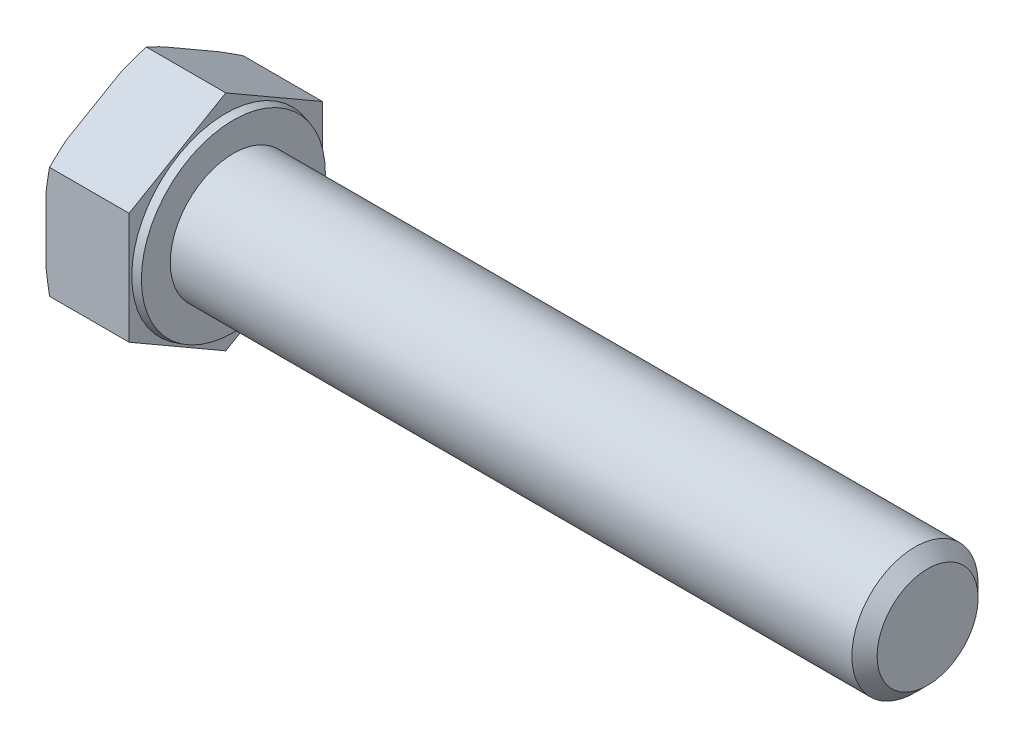
SolidWorks part; units mm, degrees
material "AISI 1020"
ref_plane "Спереди" through (0, 0, 0) normal (0, 0, 1) x (1, 0, 0)
ref_plane "Сверху" through (0, 0, 0) normal (0, 1, 0) x (1, 0, 0)
ref_plane "Справа" through (0, 0, 0) normal (1, 0, 0) x (0, 0, -1)
sketch "Эскиз1" plane through (0, 0, 0) normal (0, 0, 1) x (1, 0, 0)
  line L0 (-1000, 0) -> (49000, 0) construction
  line L1 (-6.58, 0) -> (-6.58, 8.85)
  line L2 (-6.58, 8.85) -> (0, 8.85)
  line L3 (0, 8.85) -> (0, 7.449)
  line L4 (0.6, 5) -> (55.6, 5)
  line L5 (55.6, 5) -> (55.6, 0)
  line L6 (-6.58, 0) -> (55.6, 0)
  line L7 (0, 7.449) -> (0.6, 7.2882)
  line L8 (0.6, 7.2882) -> (0.6, 5)
  line L9 (0.5, 0) -> (0.5, 7.315) construction
  dimension "_d" = 10
  dimension "D1" = 55
  dimension "D5" = 17.7
  dimension "D2" = 0.6
  dimension "D3" = 6.58
  dimension "D4" = 0.1
  dimension "D6" = 14.63
  dimension "D7" = 75
revolve "Повернуть1" add sketch "Эскиз1" angle 360 about L0
sketch "Эскиз2" plane through (-6.58, 0, 0) normal (-1, 0, 0) x (0, 0, 1)
  line L1 (0, -8.85) -> (7.6643, -4.425)
  line L2 (7.6643, -4.425) -> (7.6643, 4.425)
  line L3 (7.6643, 4.425) -> (0, 8.85)
  line L4 (0, 8.85) -> (-7.6643, 4.425)
  line L5 (-7.6643, 4.425) -> (-7.6643, -4.425)
  line L6 (-7.6643, -4.425) -> (0, -8.85)
  circle A0 centre (0, 0) radius 7.6643 construction
  circle A1 centre (0, 0) radius 8.85 construction
extrude "Вырез-Вытянуть1" cut sketch "Эскиз2" against normal through all flip side to cut
sketch "Эскиз4" plane through (0, 0, 0) normal (0, 0, 1) x (1, 0, 0)
  line L0 (-1000, 0) -> (49000, 0) construction
  line L1 (-6.58, 8.075) -> (-6.2979, 8.85)
  line L2 (-6.2979, 8.85) -> (-6.58, 8.85)
  line L3 (-6.58, 8.85) -> (-6.58, 8.075)
  line L4 (-6.58, 4.425) -> (-6.58, 8.85) construction
  line L6 (0, 8.85) -> (-6.58, 8.85) construction
  dimension "D1" = 20
  dimension "D2" = 16.15
revolve "Вырез-Повернуть1" cut sketch "Эскиз4" angle 360 about L0
chamfer "Фаска1" distance 1 angle 45 1 edges at (55.6, 0, 5)
equation "\"l\" = 55'длина болта"
equation "\"_d\"= 10'диаметр болта"
equation "\"b\"= 20'длина резьбы"
equation "\"k\"= 6.58'толщина шляпки"
equation "\"e\"= 17.7'диаметр головки описанный"
equation "\"S\"= 17'размер под ключ"
equation "\"_d@Эскиз1\"=\"_d\""
equation "\"dw\"= 14.63"
equation "\"da\"= 9.78"
equation "\"с\"= 0.6"
equation "\"D1@Эскиз1\"=\"l\""
equation "\"D5@Эскиз1\"=\"e\""
equation "\"D2@Эскиз1\"=\"с\""
equation "\"D3@Эскиз1\"=\"k\""
equation "\"D2@Эскиз4\"=\"S\"*0.95"
equation "\"D1@Фаска1\"=\"_d\"/10"
equation "\"D6@Эскиз1\"=\"dw\""
